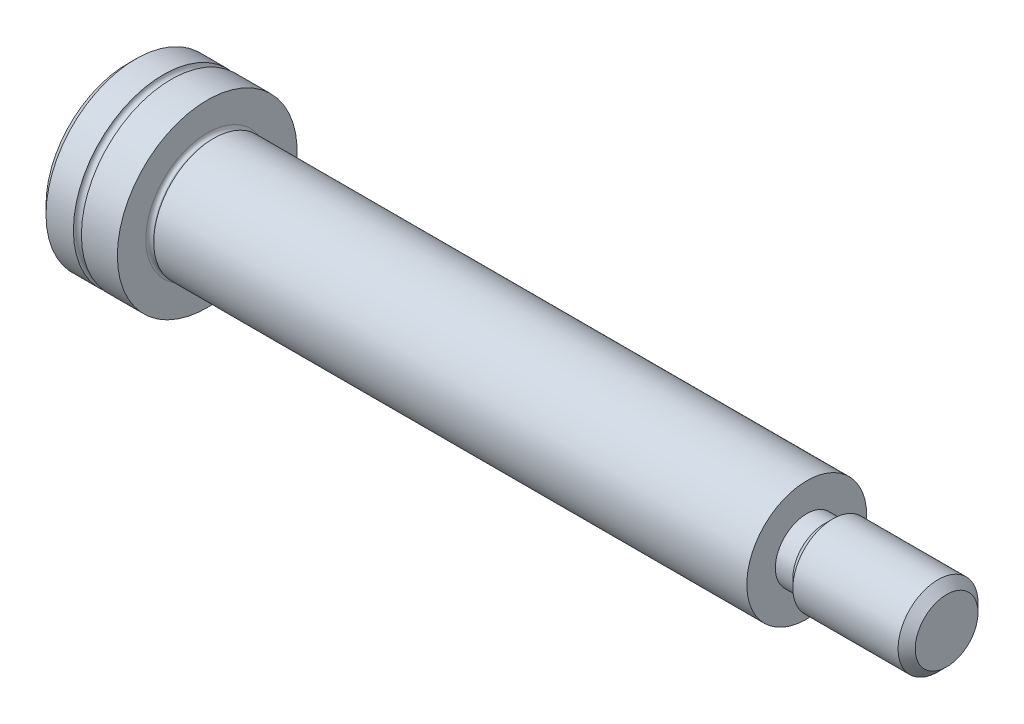
SolidWorks part; units mm, degrees
material "AISI 304"
ref_plane "Front Plane" through (0, 0, 0) normal (0, 0, 1) x (1, 0, 0)
ref_plane "Top Plane" through (0, 0, 0) normal (0, 1, 0) x (1, 0, 0)
ref_plane "Right Plane" through (0, 0, 0) normal (1, 0, 0) x (0, 0, -1)
ref_plane "Plane1" through (0, 0, 0) normal (0, 0, -1) x (-1, 0, 0)
sketch "Sketch1" plane through (0, 0, 0) normal (0, 0, -1) x (-1, 0, 0)
  line L0 (0, 4.5) -> (0, 0)
  line L1 (0, 0) -> (4, 0)
  line L2 (4, 0) -> (4, 4.5)
  line L3 (4, 4.5) -> (2.2, 4.5)
  line L4 (1.8, 4.5) -> (0, 4.5)
  line L5 (0, 0) -> (4, 0) construction
  arc A0 (2.2, 4.5) -> (1.8, 4.5) centre (2, 4.5) cw
revolve "Revolve1" add sketch "Sketch1" angle 360 about L5
sketch "Sketch2" plane through (0, 0, 0) normal (1, 0, 0) x (0, 0, -1)
  circle A0 centre (0, 0) radius 2.88
extrude "Boss-Extrude1" add sketch "Sketch2" along normal blind 0.2507
sketch "Sketch3" plane through (0.2507, 0, 0) normal (1, 0, 0) x (0, 0, -1)
  circle A0 centre (0, 0) radius 2.88
extrude "Boss-Extrude2" add sketch "Sketch3" along normal blind 0.0693 draft 60 draft outward yes
sketch "Sketch4" plane through (0.32, 0, 0) normal (1, 0, 0) x (0, 0, -1)
  circle A0 centre (0, 0) radius 3
extrude "Boss-Extrude3" add sketch "Sketch4" along normal blind 29.68
sketch "Sketch5" plane through (30, 0, 0) normal (1, 0, 0) x (0, 0, -1)
  circle A0 centre (0, 0) radius 1.5705
extrude "Boss-Extrude4" add sketch "Sketch5" along normal blind 0.875
sketch "Sketch6" plane through (30.875, 0, 0) normal (1, 0, 0) x (0, 0, -1)
  circle A0 centre (0, 0) radius 1.5705
extrude "Boss-Extrude5" add sketch "Sketch6" along normal blind 0.4295 draft 45 draft outward yes
sketch "Sketch7" plane through (31.3045, 0, 0) normal (1, 0, 0) x (0, 0, -1)
  circle A0 centre (0, 0) radius 2
extrude "Boss-Extrude6" add sketch "Sketch7" along normal blind 5.6955
sketch "Sketch8" plane through (-4, 0, 0) normal (-1, 0, 0) x (0, 0, 1)
  line L0 (1.5, -0.866) -> (1.5, 0.866)
  line L1 (1.5, 0.866) -> (0, 1.7321)
  line L2 (0, 1.7321) -> (-1.5, 0.866)
  line L3 (-1.5, 0.866) -> (-1.5, -0.866)
  line L4 (-1.5, -0.866) -> (0, -1.7321)
  line L5 (0, -1.7321) -> (1.5, -0.866)
extrude "Cut-Extrude1" cut sketch "Sketch8" against normal blind 2
sketch "Sketch9" plane through (0, 0, 0) normal (0, 0, 1) x (1, 0, 0)
  line L0 (-2, 1.44) -> (-2, 0)
  line L1 (-2, 0) -> (-1.1686, 0)
  line L2 (-1.1686, 0) -> (-2, 1.44)
  line L3 (-2, 0) -> (-1.1686, 0) construction
revolve "Cut-Revolve1" cut sketch "Sketch9" angle 360 about L3
chamfer "Chamfer1" distance 0.4295 angle 45 2 edges at (-4, 0, 4.5) (37, 0, -2)
fillet "Fillet1" radius 0.195 1 edges at (0, 0, -2.88)
